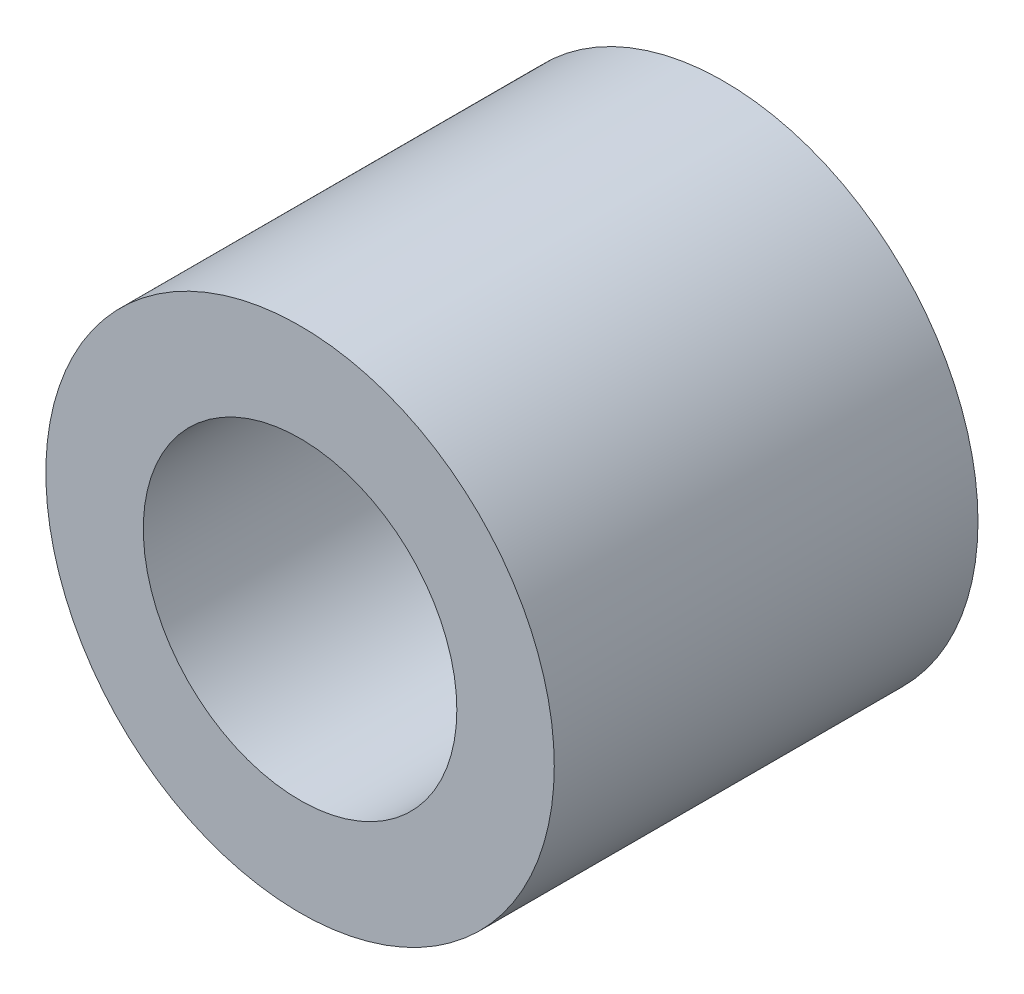
SolidWorks part; units mm, degrees
ref_plane "Front Plane" through (0, 0, 0) normal (0, 0, 1) x (1, 0, 0)
ref_plane "Top Plane" through (0, 0, 0) normal (0, 1, 0) x (1, 0, 0)
ref_plane "Right Plane" through (0, 0, 0) normal (1, 0, 0) x (0, 0, -1)
sketch "Esquisse1" plane through (0, 0, 0) normal (0, 0, 1) x (1, 0, 0)
  circle A0 centre (0, 0) radius 1.85
  circle A1 centre (0, 0) radius 3
  dimension "D1" = 6
  dimension "D2" = 3.7
extrude "Boss.-Extru.1" add sketch "Esquisse1" along normal blind 5
